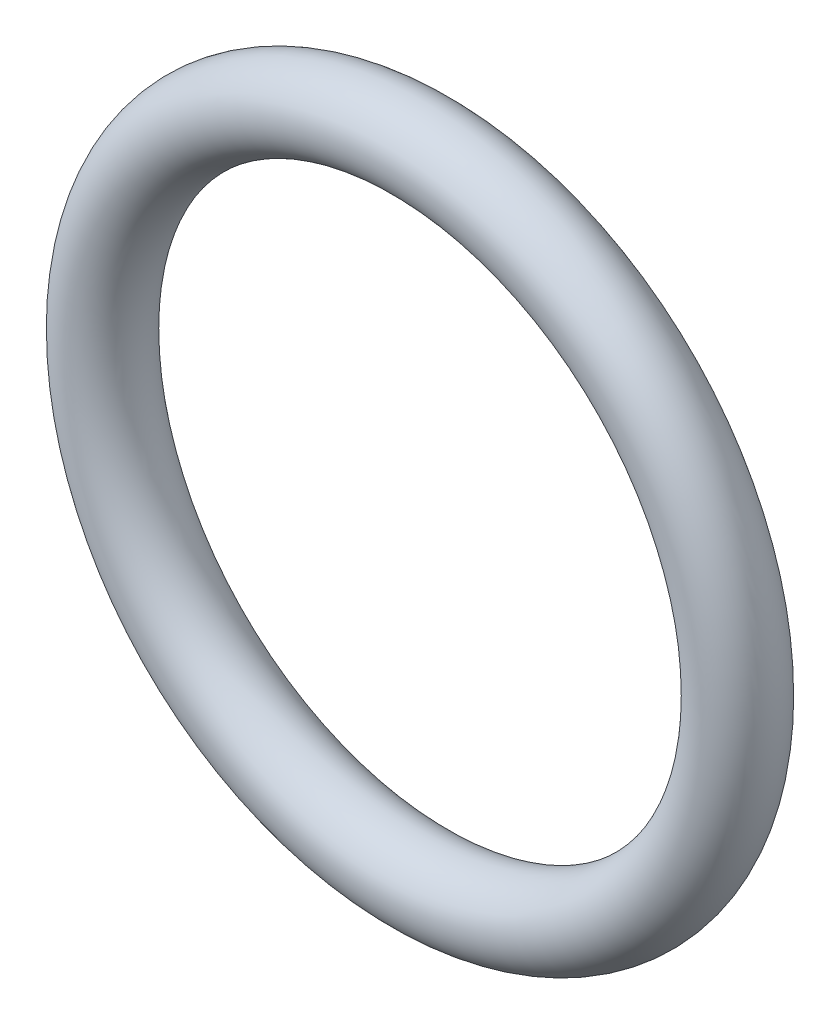
SolidWorks part; units mm, degrees
ref_plane "Front" through (0, 0, 0) normal (0, 0, 1) x (1, 0, 0)
ref_plane "Top" through (0, 0, 0) normal (0, 1, 0) x (1, 0, 0)
ref_plane "Right" through (0, 0, 0) normal (1, 0, 0) x (0, 0, -1)
sketch "Sketch1" plane through (0, 0, 0) normal (1, 0, 0) x (0, -1, 0)
  line L0 (0, -0.889) -> (0, 0.889) construction
  line L2 (-8.7871, 0) -> (8.7871, 0) construction
  line L3 (-6.2103, 0) -> (6.2103, 0) construction
  circle A0 centre (7.0993, 0) radius 0.889
  point P9 (6.2103, 0)
  point P10 (7.9883, 0)
  point P13 (7.0993, 0.889)
  point P14 (7.0993, -0.889)
  dimension "Width" = 1.778
  dimension "ID" = 12.4206
revolve "Revolve1" add sketch "Sketch1" angle 360 about L0
